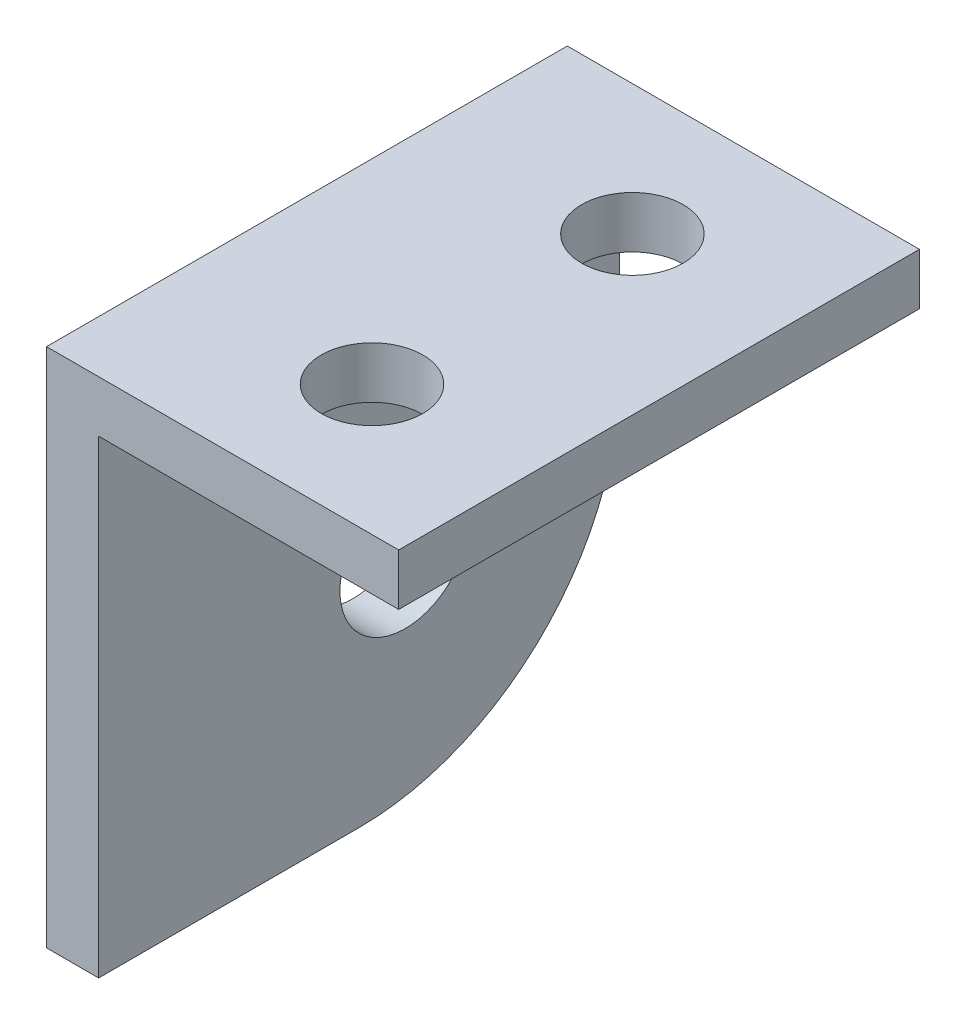
SolidWorks part; units mm, degrees
ref_plane "Front Plane" through (0, 0, 0) normal (0, 0, 1) x (1, 0, 0)
ref_plane "Top Plane" through (0, 0, 0) normal (0, 1, 0) x (1, 0, 0)
ref_plane "Right Plane" through (0, 0, 0) normal (1, 0, 0) x (0, 0, -1)
sketch "Sketch1" plane through (0, 0, 0) normal (0, 0, 1) x (1, 0, 0)
  line L4 (-12.7, -12.7) -> (-12.7, 12.7)
  line L13 (4.4768, 10.1871) -> (4.4768, 12.7)
  line L14 (4.4768, 12.7) -> (-12.7, 12.7)
  line L15 (-10.16, -12.7) -> (-12.7, -12.7)
  line L16 (-10.16, 10.1871) -> (-10.16, -12.7)
  line L17 (4.4768, 10.1871) -> (-10.16, 10.1871)
  point P0 (0, 0)
  dimension "D1" = 12.7
  dimension "D2" = 12.7
  dimension "D3" = 17.1768
  dimension "D4" = 25.4
  dimension "D5" = 2.5129
  dimension "D6" = 2.54
extrude "Boss-Extrude1" add sketch "Sketch1" along normal blind 25.4
fillet "Fillet1" radius 12.7 1 edges at (-11.43, -12.7, 0)
sketch "Sketch2" plane through (-10.16, 0, 0) normal (1, 0, 0) x (0, 0, -1)
  line L0 (-12.7, 0) -> (-3.7197, -8.9803) construction
  circle A0 centre (-5.5479, -10.5342) radius 0.0327
  circle A1 centre (-12.7, 0) radius 12.7 construction
  circle A2 centre (-10.4549, -2.2451) radius 3.175
  dimension "D2" = 6.35
  dimension "D1" = 3.175
extrude "Cut-Extrude1" cut sketch "Sketch2" against normal through all contours A2
sketch "Sketch3" plane through (0, 10.1871, 0) normal (0, -1, 0) x (1, 0, 0)
  line L0 (-10.16, 25.4) -> (4.4768, 25.4) construction
  line L1 (-12.7, 25.4) -> (-12.7, 12.7) construction
  line L2 (-12.7, 25.4) -> (-12.7, 0) construction
  circle A0 centre (-3.175, 19.05) radius 2.4765
  circle A1 centre (-3.175, 6.35) radius 2.4765
  dimension "D1" = 4.953
  dimension "D5" = 9.525
  dimension "D2" = 12.7
  dimension "D3" = 6.35
  dimension "D4" = 9.525
extrude "Cut-Extrude2" cut sketch "Sketch3" against normal through all
